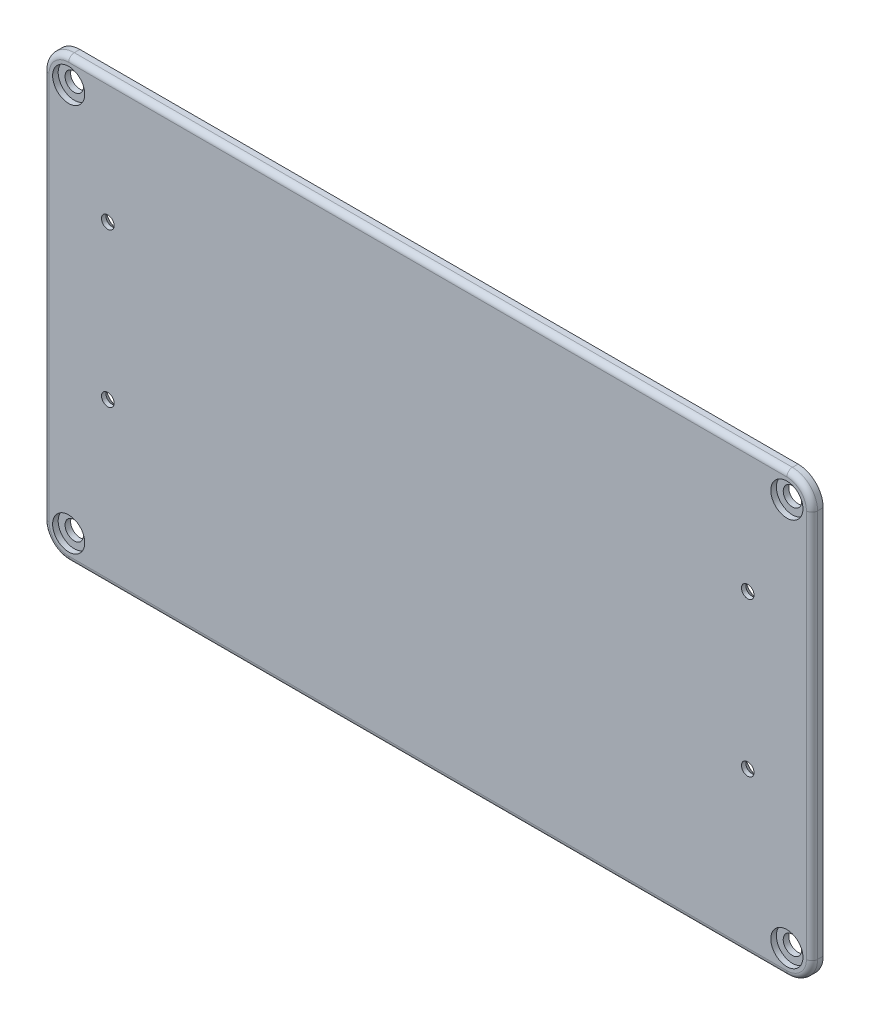
SolidWorks part; units mm, degrees
ref_plane "Plan de face" through (0, 0, 0) normal (0, 0, 1) x (1, 0, 0)
ref_plane "Plan de dessus" through (0, 0, 0) normal (0, 1, 0) x (1, 0, 0)
ref_plane "Plan de droite" through (0, 0, 0) normal (1, 0, 0) x (0, 0, -1)
sketch "Esquisse4" plane through (0, 0, 0) normal (0, 0, 1) x (1, 0, 0)
  line L0 (-137.5, 78.5) -> (-137.5, -78.5)
  line L1 (-137.5, -78.5) -> (137.5, -78.5)
  line L2 (0, -2.2) -> (0, 2.2) construction
  line L3 (137.5, 78.5) -> (137.5, -78.5)
  line L4 (2.2, 0) -> (-2.2, 0) construction
  line L5 (-137.5, 78.5) -> (137.5, 78.5)
  dimension "D1" = 157
  dimension "D2" = 275
extrude "Boss.-Extru.2" add sketch "Esquisse4" along normal blind 4
sketch "Esquisse5" plane through (0, 0, 0) normal (0, 0, -1) x (-1, 0, 0)
  line L0 (-114.5, 78.5) -> (-114.5, -78.5) construction
  line L1 (-137.5, 78.5) -> (137.5, 78.5) construction
  line L2 (137.5, -78.5) -> (-137.5, -78.5) construction
  line L3 (-137.5, -78.5) -> (-137.5, 78.5) construction
  line L4 (0, 2.2) -> (0, -2.2) construction
  point P8 (-114.5, 34)
  point P9 (-114.5, -21)
  point P12 (114.5, 34)
  point P13 (114.5, -21)
  dimension "D1" = 23
  dimension "D2" = 44.5
  dimension "D3" = 57.5
hole_wizard "Fraisage pour vis à tête fraisée M42" positions "Esquisse5" profile "Esquisse6" countersink size "M4" standard "Ansi Metric" end condition through all
sketch "Esquisse6" plane through (-114.5, -21, 0) normal (1, 0, 0) x (0, 1, 0)
  line L0 (0, 0) -> (0, 4)
  line L1 (0, 4) -> (2.25, 4)
  line L2 (2.25, 4) -> (2.25, 2.45)
  line L3 (2.25, 2.45) -> (4.7, 0)
  line L5 (4.7, 0) -> (0, 0)
  line L6 (-2.25, 2.45) -> (-4.7, 0) construction
  line L11 (0, -6.35) -> (0, 107.95) construction
  dimension "Diamètre du perçage jusqu'au prochain" = 4.5
  dimension "Profondeur du perçage jusqu'au prochain" = 4
  dimension "Diamètre du fraisage entrant" = 9.4
  dimension "Angle du fraisage entrant" = 90
sketch "Esquisse7" plane through (0, 0, 4) normal (0, 0, 1) x (1, 0, 0)
  line L0 (-137.5, -69.5) -> (-128.5, -69.5) construction
  line L1 (-137.5, 78.5) -> (-137.5, -78.5) construction
  line L2 (-128.5, -69.5) -> (-128.5, -78.5) construction
  line L3 (-137.5, -78.5) -> (137.5, -78.5) construction
  line L4 (2.2, 0) -> (-2.2, 0) construction
  line L5 (0, -2.2) -> (0, 2.2) construction
  point P8 (-128.5, -69.5)
  point P10 (-128.5, 69.5)
  point P14 (128.5, 69.5)
  point P15 (128.5, -69.5)
  dimension "D1" = 9
  dimension "D2" = 9
hole_wizard "Chambrage pour Vis à tête ronde à 6 pans creux M61" positions "Esquisse7" profile "Esquisse8" counterbore size "M6" standard "Ansi Metric" end condition through all
sketch "Esquisse8" plane through (128.5, -69.5, 4) normal (1, 0, 0) x (0, -1, 0)
  line L0 (0, 0) -> (0, 4)
  line L1 (0, 4) -> (3.3, 4)
  line L3 (3.3, 4) -> (3.3, 2)
  line L4 (3.3, 2) -> (5.75, 2)
  line L5 (5.75, 2) -> (5.75, 0)
  line L7 (5.75, 0) -> (0, 0)
  line L11 (0, -6.35) -> (0, 107.95) construction
  dimension "Diamètre du perçage jusqu'au prochain" = 6.6
  dimension "Profondeur du perçage jusqu'au prochain" = 4
  dimension "Diamètre du chambrage" = 11.5
  dimension "Profondeur du chambrage" = 2
fillet "Congé1" radius 9 4 edges at (137.5, 78.5, 2) (137.5, -78.5, 2) (-137.5, 78.5, 2) (-137.5, -78.5, 2)
fillet "Congé2" radius 2 8 edges at (-134.864, -75.864, 4) (-137.5, 0, 4) (-134.864, 75.864, 4) (0, 78.5, 4) (134.864, 75.864, 4) (137.5, 0, 4) (134.864, -75.864, 4) (0, -78.5, 4)
